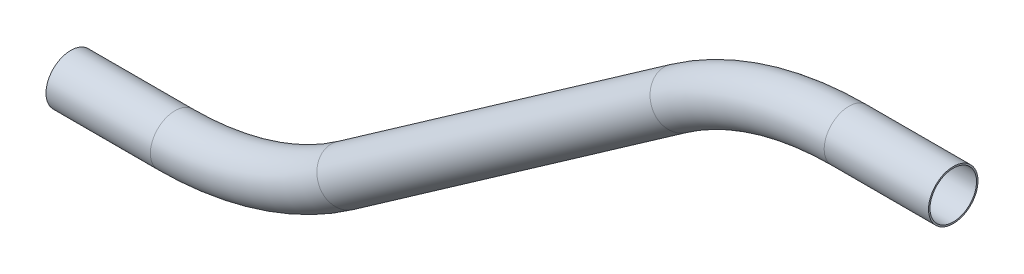
SolidWorks part; units mm, degrees
material "6061 Alloy"
ref_plane "Front Plane" through (0, 0, 0) normal (0, 0, 1) x (1, 0, 0)
ref_plane "Top Plane" through (0, 0, 0) normal (0, 1, 0) x (1, 0, 0)
ref_plane "Right Plane" through (0, 0, 0) normal (1, 0, 0) x (0, 0, -1)
sketch "Sketch4" plane through (0, 0, 0) normal (0, 0, 1) x (1, 0, 0)
  line L0 (95.0917, 47.4325) -> (121.8659, 47.4325)
  line L2 (51.3852, 33.6519) -> (-34.0921, -26.1999)
  line L3 (-34.0921, -26.1999) -> (71.0659, 47.4325)
  line L4 (121.8659, 47.4325) -> (71.0659, 47.4325)
  line L5 (-77.7986, -39.9805) -> (-104.5728, -39.9805)
  line L6 (-104.5728, -39.9805) -> (-53.7728, -39.9805)
  line L7 (51.3852, 33.6519) -> (-53.7728, -39.9805)
  arc A0 (95.0917, 47.4325) -> (51.3852, 33.6519) centre (95.0917, -28.7675) ccw
  arc A1 (-34.0921, -26.1999) -> (-77.7986, -39.9805) centre (-77.7986, 36.2195) cw
  point P9 (71.0659, 47.4325)
  point P14 (-53.7728, -39.9805)
  dimension "D3" = 35
  dimension "D4" = 35
  dimension "D1" = 76.2
  dimension "D2" = 76.2
  dimension "D5" = 152.4
  dimension "D6" = 50.8
  dimension "D7" = 50.8
ref_plane "Plane2" through (121.8659, 47.4325, 0) normal (-1, 0, 0) x (0, 0, 1)
sketch "Sketch5" plane through (121.8659, 47.4325, 0) normal (-1, 0, 0) x (0, 0, 1)
  circle A0 centre (0, 0) radius 5.969
  circle A1 centre (0, 0) radius 6.35
  dimension "D1" = 12.7
  dimension "D2" = 11.938
sweep "Sweep1" add profiles "Sketch5" path "Sketch4"
sketch "Sketch6" plane through (-104.5728, 0, 0) normal (-1, 0, 0) x (0, 0, 1)
  line L0 (-6.35, -39.9805) -> (6.35, -39.9805) construction
sketch "Sketch7" plane through (0, 0, 0) normal (0, 0, 1) x (1, 0, 0)
  line L0 (-104.5728, -39.9805) -> (-136.2487, -39.9805) construction
  line L1 (-104.5728, -30.4555) -> (-104.5728, -49.5055) construction
